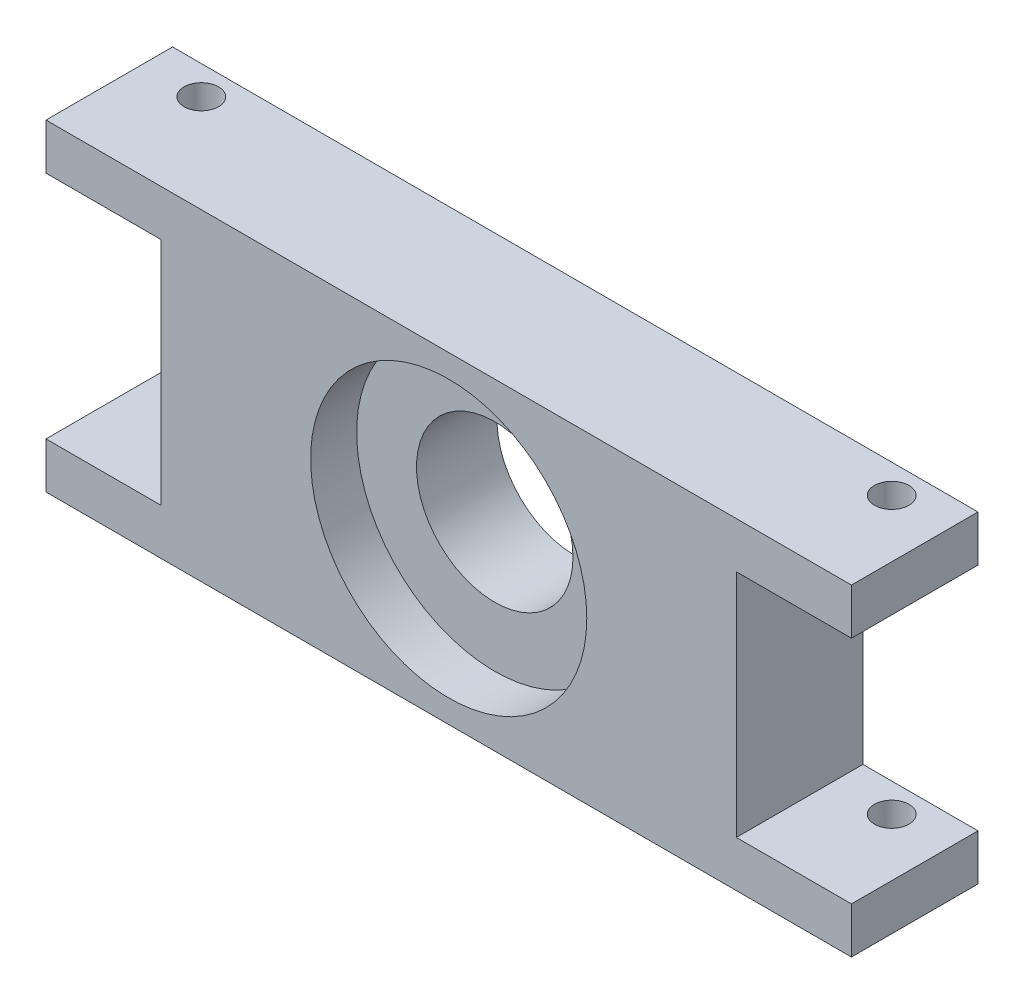
SolidWorks part; units mm, degrees
ref_plane "Plan de face" through (0, 0, 0) normal (0, 0, 1) x (1, 0, 0)
ref_plane "Plan de dessus" through (0, 0, 0) normal (0, 1, 0) x (1, 0, 0)
ref_plane "Plan de droite" through (0, 0, 0) normal (1, 0, 0) x (0, 0, -1)
sketch "Esquisse1" plane through (0, 0, 0) normal (0, 0, 1) x (1, 0, 0)
  line L1 (-35, 14) -> (35, 14)
  line L2 (-35, 14) -> (-35, -14)
  line L3 (-35, -14) -> (35, -14)
  line L4 (35, 14) -> (35, -14)
  dimension "D1" = 70
  dimension "D2" = 28
  dimension "D3" = 14
  dimension "D4" = 35
extrude "Boss.-Extru.1" add sketch "Esquisse1" along normal blind 11
sketch "Esquisse2" plane through (0, 14, 0) normal (0, 1, 0) x (1, 0, 0)
  line L0 (35, -11) -> (35, 0) construction
  line L1 (35, 0) -> (-35, 0) construction
  circle A0 centre (30, -2.5) radius 1.5
  circle A1 centre (-30, -2.5) radius 1.5
  dimension "D1" = 5
  dimension "D3" = 3
  dimension "D4" = 60
  dimension "D5" = 3
  dimension "D2" = 2.5
extrude "Enlèv. mat.-Extru.1" cut sketch "Esquisse2" against normal through all
sketch "Esquisse3" plane through (0, 0, 11) normal (0, 0, 1) x (1, 0, 0)
  circle A0 centre (0, 0) radius 6.8
  dimension "D1" = 13.6
extrude "Enlèv. mat.-Extru.2" cut sketch "Esquisse3" against normal through all
sketch "Esquisse4" plane through (0, 0, 11) normal (0, 0, 1) x (1, 0, 0)
  circle A0 centre (0, 0) radius 12
  dimension "D1" = 24
extrude "Enlèv. mat.-Extru.3" cut sketch "Esquisse4" against normal blind 4
sketch "Esquisse5" plane through (0, 0, 11) normal (0, 0, 1) x (1, 0, 0)
  line L1 (-35, 10) -> (-25, 10)
  line L2 (-35, 10) -> (-35, -10)
  line L3 (-35, -10) -> (-25, -10)
  line L4 (-25, 10) -> (-25, -10)
  line L5 (35, 14) -> (-35, 14) construction
  line L6 (-35, -14) -> (35, -14) construction
  line L9 (-35, 14) -> (-35, -14) construction
  dimension "D1" = 10
  dimension "D2" = 4
  dimension "D3" = 4
extrude "Enlèv. mat.-Extru.4" cut sketch "Esquisse5" against normal through all
sketch "Esquisse6" plane through (0, 0, 11) normal (0, 0, 1) x (1, 0, 0)
  line L0 (-25, 10) -> (-35, 10) construction
  line L1 (25, 10) -> (35, 10)
  line L2 (25, 10) -> (25, -10)
  line L3 (25, -10) -> (35, -10)
  line L4 (35, 10) -> (35, -10)
  line L5 (-35, -10) -> (-25, -10) construction
  line L6 (35, -14) -> (35, 14) construction
  dimension "D1" = 10
extrude "Enlèv. mat.-Extru.5" cut sketch "Esquisse6" against normal through all
